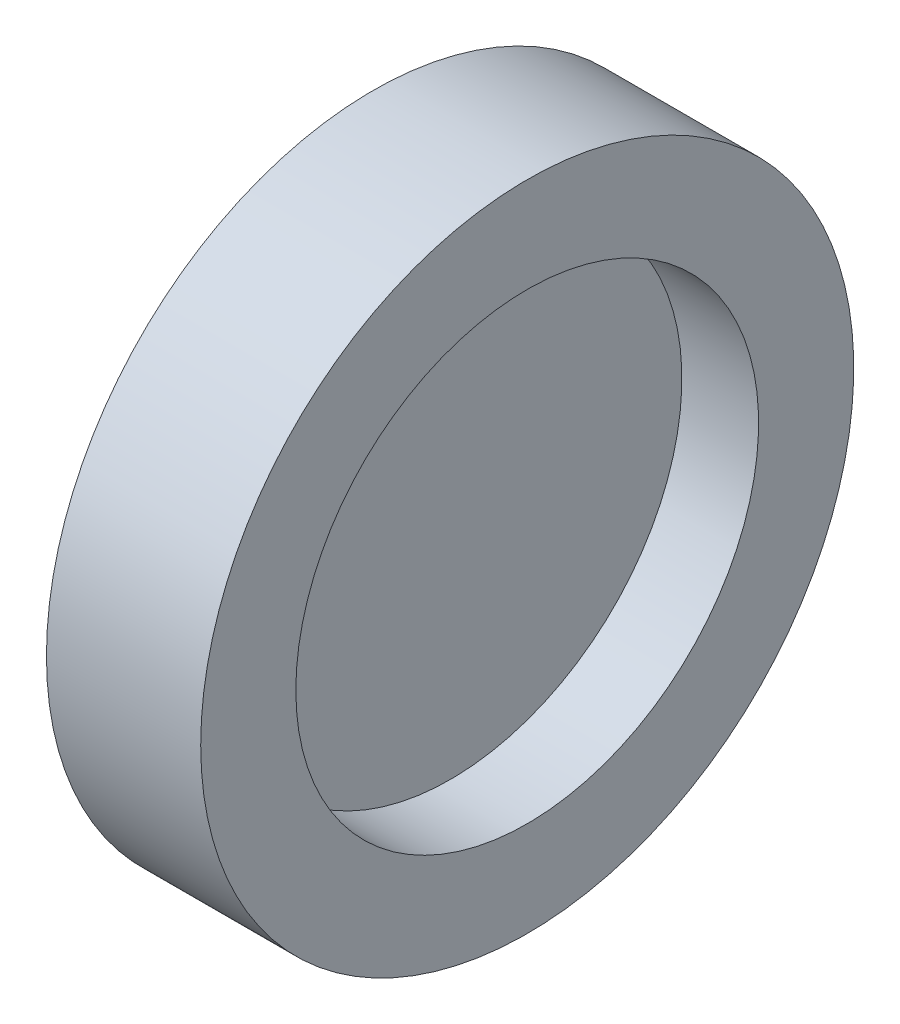
SolidWorks part; units mm, degrees
ref_plane "前视基准面" through (0, 0, 0) normal (0, 0, 1) x (1, 0, 0)
ref_plane "上视基准面" through (0, 0, 0) normal (0, 1, 0) x (1, 0, 0)
ref_plane "右视基准面" through (0, 0, 0) normal (1, 0, 0) x (0, 0, -1)
sketch "草图1" plane through (0, 0, 0) normal (0, 0, 1) x (1, 0, 0)
  line L0 (-0.015, 9) -> (-0.015, 0)
  line L2 (-0.015, 9) -> (0.015, 9)
  line L3 (-0.015, 0) -> (0.015, 0)
  line L4 (0.015, 9) -> (0.015, 0)
revolve "旋转2" add sketch "草图1" angle 360 about L3
sketch "草图4" plane through (0, 0, 0) normal (0, 0, 1) x (1, 0, 0)
  line L0 (-3, 12.7) -> (3, 12.7)
  line L1 (3, 12.7) -> (3, 9)
  line L2 (3, 9) -> (-3, 9)
  line L3 (0.015, 9) -> (-0.015, 9) construction
  line L4 (-3, 9) -> (-3, 12.7)
  line L5 (0, 9) -> (0, 12.7) construction
  line L6 (-1.6142, 0) -> (1.5903, 0) construction
revolve "旋转3" add sketch "草图4" angle 360 about L6
equation "\"D1@草图4\"=\"D1@草图1\""
